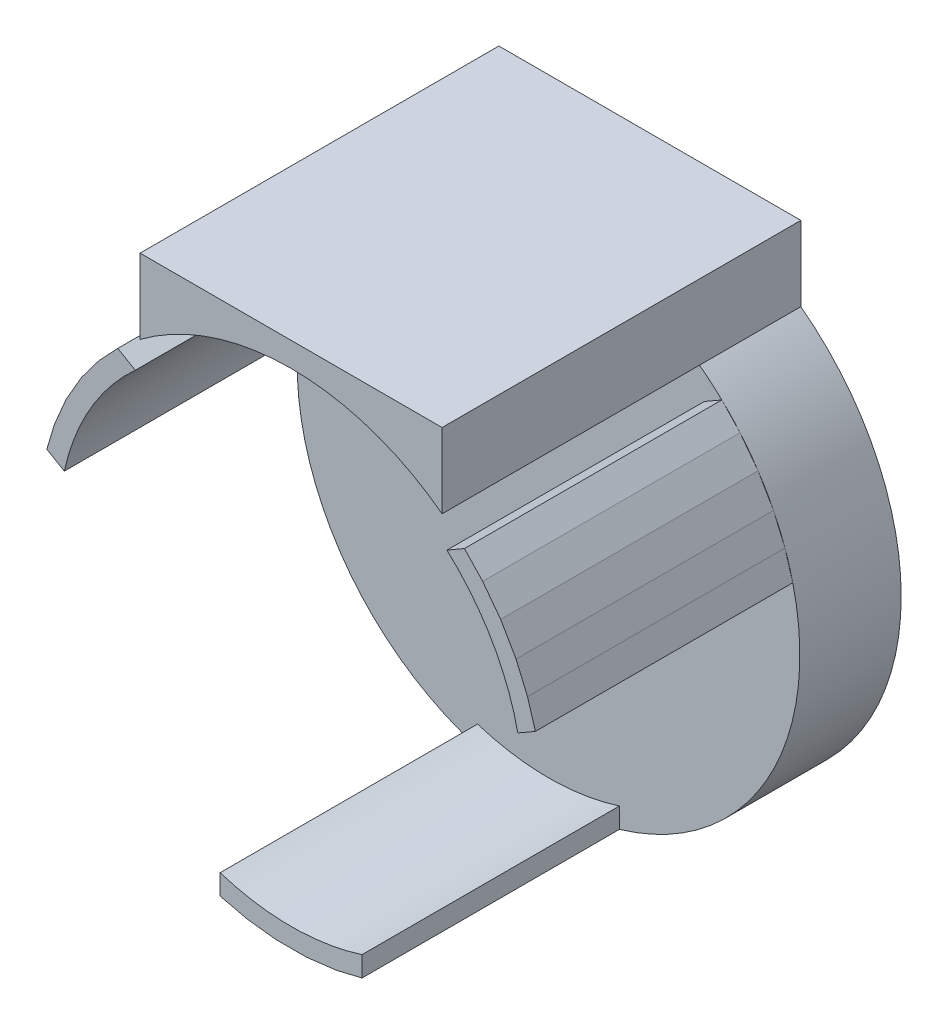
SolidWorks part; units mm, degrees
ref_plane "Front Plane" through (0, 0, 0) normal (0, 0, 1) x (1, 0, 0)
ref_plane "Top Plane" through (0, 0, 0) normal (0, 1, 0) x (1, 0, 0)
ref_plane "Right Plane" through (0, 0, 0) normal (1, 0, 0) x (0, 0, -1)
sketch "Sketch1" plane through (0, 0, 0) normal (0, 0, 1) x (1, 0, 0)
  line L0 (0, 13.6) -> (0, 8.52) construction
  line L2 (-7.45, 9.9125) -> (-7.45, 13.6)
  line L3 (-7.45, 13.6) -> (7.45, 13.6)
  line L4 (7.45, 9.9125) -> (7.45, 13.6)
  arc A0 (-7.45, 9.9125) -> (7.45, 9.9125) centre (0, 0) ccw
  dimension "D1" = 24.8
  dimension "D2" = 13.6
  dimension "D4" = 14.9
  dimension "D5" = 0
sketch "Sketch2" plane through (0, 0, 0) normal (0, 0, 1) x (1, 0, 0)
  line L1 (-13.3337, -13.3837) -> (13.4823, -13.3837)
  line L2 (-13.3337, -13.3837) -> (-13.3337, 14.918)
  line L3 (-13.3337, 14.918) -> (13.4823, 14.918)
  line L4 (13.4823, -13.3837) -> (13.4823, 14.918)
extrude "Square extrude" add sketch "Sketch2" along normal blind 5
extrude "Actual shape cut" cut sketch "Sketch1" along normal blind 5 thin thin type one direction wall 10
sketch "Sketch3" plane through (0, 0, 5) normal (0, 0, 1) x (1, 0, 0)
  line L0 (0, 0) -> (0, -13.6065) construction
  line L3 (-7.45, 13.6) -> (7.45, 13.6)
  line L5 (3.5, -11.8958) -> (3.5, -10.8958)
  line L6 (-3.5, -11.8958) -> (-3.5, -10.8958)
  line L7 (3.5, -11.8958) -> (2.2269, -12.1984)
  line L8 (2.2269, -12.1984) -> (0.7597, -12.3767)
  line L9 (0.7597, -12.3767) -> (-0.7597, -12.3767)
  line L10 (-0.7597, -12.3767) -> (-2.1874, -12.2055)
  line L11 (-2.1874, -12.2055) -> (-3.5, -11.8958)
  line L12 (-7.45, 13.6) -> (-7.45, 9.9125)
  line L13 (-7.45, 9.9125) -> (7.45, 9.9125)
  line L14 (7.45, 9.9125) -> (7.45, 13.6)
  line L15 (-12.0521, 2.9168) -> (-11.186, 2.4168)
  line L16 (-8.5521, 8.979) -> (-7.686, 8.479)
  line L17 (-9.4766, 7.9971) -> (-8.5521, 8.979)
  line L18 (-10.3387, 6.8463) -> (-9.4766, 7.9971)
  line L19 (-11.0984, 5.5304) -> (-10.3387, 6.8463)
  line L20 (-11.6776, 4.1707) -> (-11.0984, 5.5304)
  line L21 (-12.0521, 2.9168) -> (-11.6776, 4.1707)
  line L22 (8.5521, 8.979) -> (7.686, 8.479)
  line L23 (12.0521, 2.9168) -> (11.186, 2.4168)
  line L24 (11.664, 4.2084) -> (12.0521, 2.9168)
  line L25 (11.0984, 5.5304) -> (11.664, 4.2084)
  line L26 (10.3387, 6.8463) -> (11.0984, 5.5304)
  line L27 (9.4507, 8.0277) -> (10.3387, 6.8463)
  line L28 (8.5521, 8.979) -> (9.4507, 8.0277)
  arc A0 (-7.45, 9.9125) -> (7.45, 9.9125) centre (0, 0) ccw construction
  arc A1 (-3.5, -10.8958) -> (3.5, -10.8958) centre (0, 0) ccw
  arc A2 (-7.686, 8.479) -> (-11.186, 2.4168) centre (0, 0) ccw
  arc A3 (11.186, 2.4168) -> (7.686, 8.479) centre (0, 0) ccw
  dimension "D1" = 1
  dimension "D2" = 3.5
  dimension "D3" = 3
extrude "Stoppers extrude" add sketch "Sketch3" along normal blind 12.7
sketch "Sketch4" plane through (0, 0, 17.7) normal (0, 0, 1) x (1, 0, 0)
  line L0 (-7.45, 9.9125) -> (7.45, 9.9125) construction
  line L1 (-7.45, 9.9125) -> (7.45, 9.9125)
  arc A1 (-7.45, 9.9125) -> (7.45, 9.9125) centre (0, 0) cw
extrude "Curve cut" cut sketch "Sketch4" against normal blind 12.7
